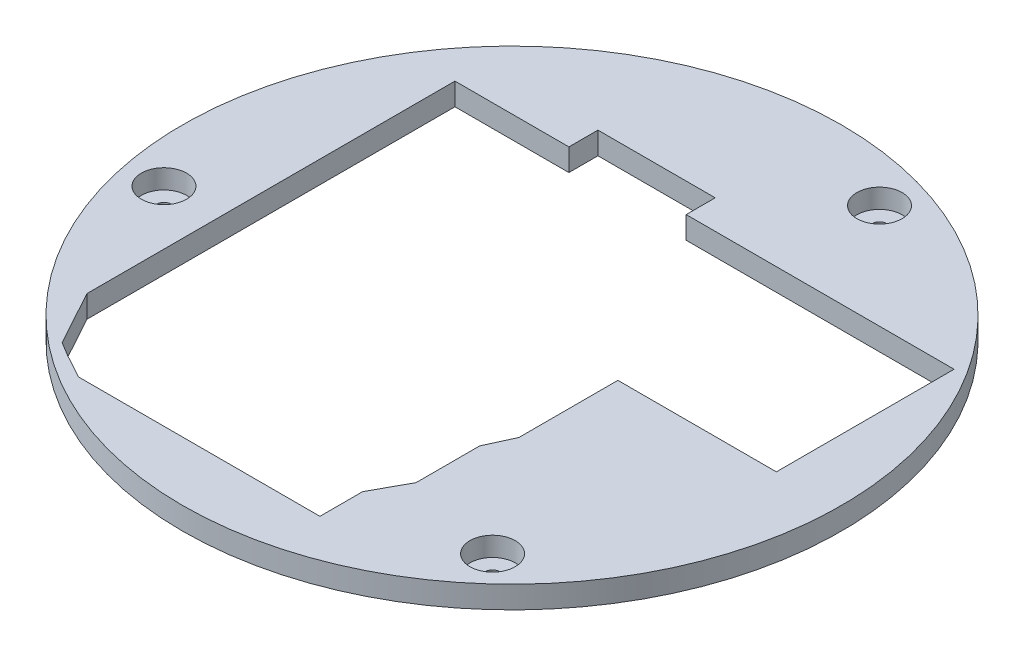
SolidWorks part; units mm, degrees
ref_plane "Front Plane" through (0, 0, 0) normal (0, 0, 1) x (1, 0, 0)
ref_plane "Top Plane" through (0, 0, 0) normal (0, 1, 0) x (1, 0, 0)
ref_plane "Right Plane" through (0, 0, 0) normal (1, 0, 0) x (0, 0, -1)
sketch "Sketch2" plane through (0, 0, 0) normal (0, 1, 0) x (1, 0, 0)
  line L0 (285.0547, 411.8953) -> (379.8385, 411.8953) construction
  line L1 (-25.3062, 23.4664) -> (-9.9565, 23.4664)
  line L2 (-9.9565, 23.4664) -> (-9.9565, 27.3791)
  line L3 (-9.9565, 27.3791) -> (5.8447, 27.3791)
  line L4 (5.8447, 27.3791) -> (5.8447, 23.4664)
  line L7 (5.8447, 23.4664) -> (41.9368, 23.4664)
  line L9 (41.9368, 23.4664) -> (41.9368, -0.4739)
  line L11 (20.5827, -13.8176) -> (18.9229, -17.4336)
  line L12 (18.9229, -17.4336) -> (18.9229, -26.0131)
  line L13 (18.9229, -26.0131) -> (16.3767, -30.6498)
  line L14 (16.3767, -30.6498) -> (16.3767, -36.409)
  line L15 (16.3767, -36.409) -> (-16.1676, -36.409)
  line L16 (-16.1676, -36.409) -> (-19.4141, -34.6262)
  line L19 (-22.6866, -30.9019) -> (-25.3062, -26.1116)
  line L20 (-25.3062, -26.1116) -> (-25.3062, 23.4664)
  line L21 (20.5827, -13.8176) -> (20.5827, -0.4739)
  line L22 (20.5827, -0.4739) -> (41.9368, -0.4739)
  line L23 (-22.6866, -30.9019) -> (-21.2617, -33.5074)
  line L24 (-21.2617, -33.5074) -> (-19.4141, -34.6262)
  circle A0 centre (5.8447, 0) radius 44.4
  dimension "D1" = 88.8
extrude "Boss-Extrude1" add sketch "Sketch2" along normal blind 3
sketch "Sketch3" plane through (0, 0, 0) normal (0, 1, 0) x (1, 0, 0)
  line L0 (5.8447, 0) -> (17.8189, 37.5363) construction
  line L1 (5.8447, 0) -> (32.365, -29.1382) construction
  line L3 (-32.6499, -8.3982) -> (5.8447, 0) construction
  circle A0 centre (5.8447, 0) radius 39.4 construction
  circle A1 centre (5.8447, 0) radius 44.4 construction
  circle A2 centre (32.365, -29.1382) radius 3.05
  circle A3 centre (17.8189, 37.5363) radius 3.05
  circle A4 centre (-32.6499, -8.3982) radius 3.05
  dimension "D3" = 5
  dimension "D4" = 6.1
  dimension "D1" = 120
  dimension "D2" = 120
extrude "Cut-Extrude3" cut sketch "Sketch3" against normal blind 2.6 from surface at 3 starting at face at (5.8447, 3, 44.4)
sketch "Sketch4" plane through (0, 0.4, 0) normal (0, 1, 0) x (1, 0, 0)
  circle A3 centre (-32.6499, -8.3982) radius 1
  circle A5 centre (17.8189, 37.5363) radius 1
  circle A7 centre (32.365, -29.1382) radius 1
  dimension "D1" = 2
extrude "Cut-Extrude4" cut sketch "Sketch4" against normal through all
